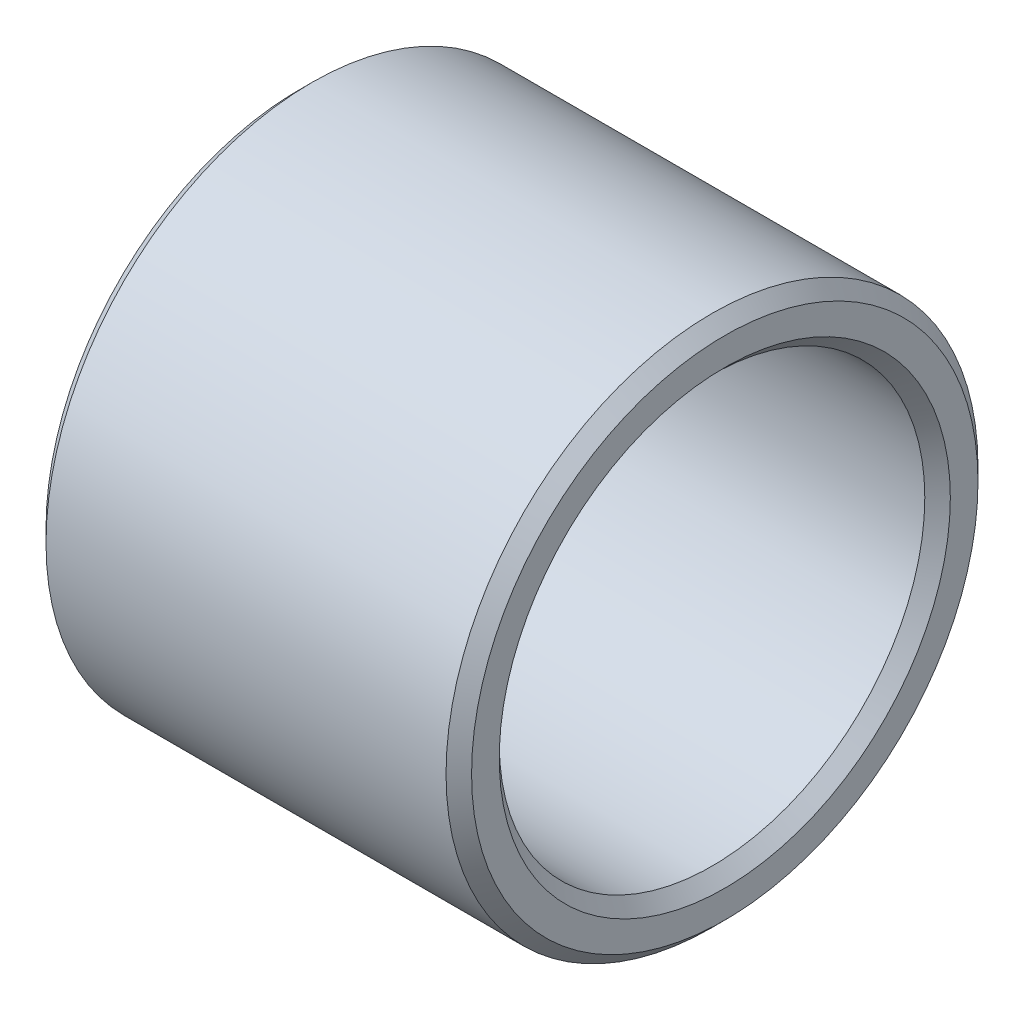
SolidWorks part; units mm, degrees
material "Brass"
ref_plane "Front Plane" through (0, 0, 0) normal (0, 0, 1) x (1, 0, 0)
ref_plane "Top Plane" through (0, 0, 0) normal (0, 1, 0) x (1, 0, 0)
ref_plane "Right Plane" through (0, 0, 0) normal (1, 0, 0) x (0, 0, -1)
sketch "Sketch1" plane through (0, 0, 0) normal (1, 0, 0) x (0, 0, -1)
  circle A0 centre (0, 0) radius 15.875
  circle A1 centre (0, 0) radius 12.7
  dimension "D1" = 25.4
  dimension "D2" = 31.75
extrude "Boss-Extrude1" add sketch "Sketch1" along normal blind 25.4
chamfer "Chamfer1" distance 0.762 angle 45 4 edges at (25.4, 0, -12.7) (25.4, 0, -15.875) (0, 0, -12.7) (0, 0, -15.875)
